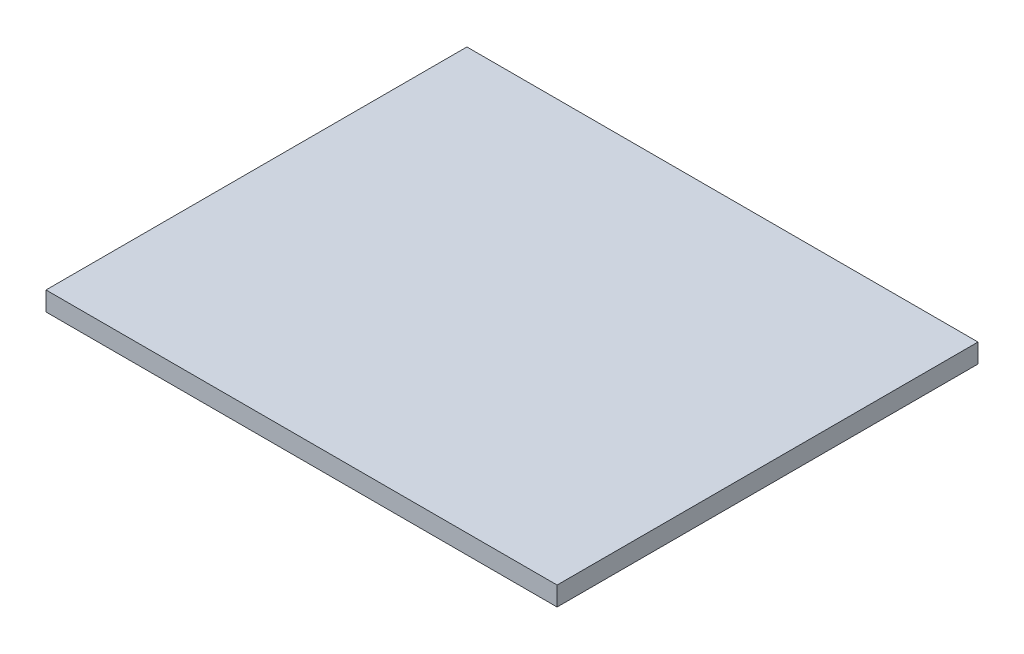
SolidWorks part; units mm, degrees
ref_plane "Front Plane" through (0, 0, 0) normal (0, 0, 1) x (1, 0, 0)
ref_plane "Top Plane" through (0, 0, 0) normal (0, 1, 0) x (1, 0, 0)
ref_plane "Right Plane" through (0, 0, 0) normal (1, 0, 0) x (0, 0, -1)
sketch "Sketch1" plane through (0, 0, 0) normal (0, 1, 0) x (1, 0, 0)
  line L1 (0, 0) -> (85, 0)
  line L2 (0, 0) -> (0, 70)
  line L3 (0, 70) -> (85, 70)
  line L4 (85, 0) -> (85, 70)
  dimension "D1" = 85
  dimension "D2" = 70
extrude "Boss-Extrude1" add sketch "Sketch1" along normal blind 3.175
